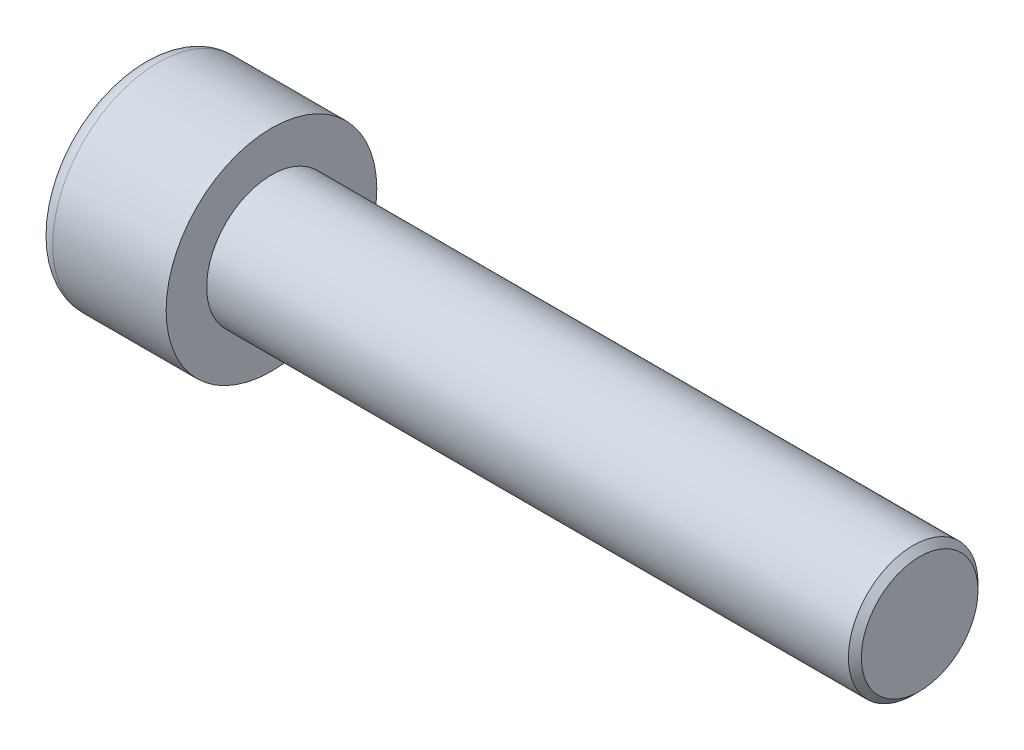
SolidWorks part; units mm, degrees
ref_plane "Front" through (0, 0, 0) normal (0, 0, 1) x (1, 0, 0)
ref_plane "Top" through (0, 0, 0) normal (0, 1, 0) x (1, 0, 0)
ref_plane "Right" through (0, 0, 0) normal (1, 0, 0) x (0, 0, -1)
sketch "Sketch1" plane through (0, 0, 0) normal (1, 0, 0) x (0, 0, -1)
  circle A0 centre (0, 0) radius 6.5
  dimension "dk" = 13
extrude "BaseHead" add sketch "Sketch1" along normal blind 8
sketch "Sketch2" plane through (8, 0, 0) normal (1, 0, 0) x (0, 0, -1)
  circle A0 centre (0, 0) radius 4
  dimension "d" = 8
extrude "BaseBody" add sketch "Sketch2" along normal blind 40
cosmetic thread "ThreadCosmetic1" parameters "b"=28, "D2"=6.647
sketch "Sketch3" plane through (0, 0, 0) normal (1, 0, 0) x (0, 0, -1)
  line L1 (3.4641, 0) -> (1.7321, 3)
  line L2 (1.7321, 3) -> (-1.7321, 3)
  line L3 (-1.7321, 3) -> (-3.4641, 0)
  line L4 (-3.4641, 0) -> (-1.7321, -3)
  line L5 (-1.7321, -3) -> (1.7321, -3)
  line L6 (1.7321, -3) -> (3.4641, 0)
  circle A0 centre (0, 0) radius 3 construction
  dimension "s" = 6
  dimension "e" = 6.9282
extrude "HexagonSocket" cut sketch "Sketch3" along normal blind 4
sketch "Sketch4" plane through (-4.1961, 0.75, 0) normal (0, 0, 1) x (-1, 0, 0)
  line L0 (-8.1961, 3.75) -> (-9.9282, 0.75)
  line L2 (-9.9282, 0.75) -> (-8.1961, 0.75)
  line L3 (-8.1961, 0.75) -> (-8.1961, 3.75)
  line L4 (-5.0351, 0.75) -> (0.839, 0.75) construction
  line L5 (-52.1961, 0.75) -> (-12.1961, 0.75) construction
  line L6 (-12.1961, 0.75) -> (-4.1961, 0.75) construction
  dimension "m" = 60
revolve "Cut-Revolve1" cut sketch "Sketch4" angle 360 about L4
fillet "HeadFillet" [suppressed] radius 0.4
fillet "TopFillet" radius 1 1 edges at (0, 0, -6.5)
chamfer "Chamfer1" distance 0.4 angle 45 1 edges at (48, 0, -4)
sketch "Sketch5" plane through (0, 0, 0) normal (0, 0, 1) x (1, 0, 0)
  line L0 (47.6, 3.4141) -> (47.9383, 4)
  line L1 (47.9383, 4) -> (47.9383, 4.6765)
  line L2 (47.9383, 4.6765) -> (47.2618, 4.6765)
  line L3 (47.2618, 4.6765) -> (47.2618, 4)
  line L4 (47.2618, 4) -> (47.6, 3.4141)
  line L5 (0, 0) -> (7.8886, 0) construction
  line L6 (47.6, -4) -> (47.6, 4) construction
  dimension "D1" = 8
  dimension "D2" = 0.6765
revolve "Cut-Revolve10" [suppressed] cut sketch "Sketch5" angle 360 about L5
pattern_linear "LPattern10" [suppressed] count 34 spacing 0.8118 along (1, 0, 0)
equation "\"r1@TopFillet\" = \"d@Sketch2\" / 8"
equation "\"D1@Chamfer1\" = \"r@HeadFillet\""
equation "\"D1@Sketch5\" = \"d@Sketch2\""
equation "\"D2@Sketch5\" =  ( \"d@Sketch2\" - \"D2@ThreadCosmetic1\" )  / 2"
equation "\"D3@LPattern10\" = \"D2@Sketch5\" * 1.2"
equation "\"D1@LPattern10\" = \"b@ThreadCosmetic1\" / \"D3@LPattern10\""
